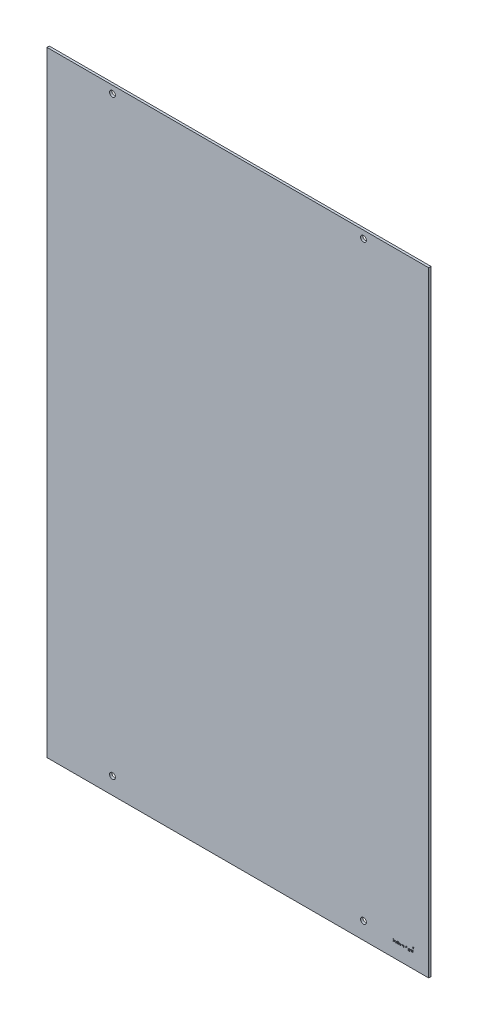
SolidWorks part; units mm, degrees
material "Acrylic (Medium-high impact)"
ref_plane "Front Plane" through (0, 0, 0) normal (0, 0, 1) x (1, 0, 0)
ref_plane "Top Plane" through (0, 0, 0) normal (0, 1, 0) x (1, 0, 0)
ref_plane "Right Plane" through (0, 0, 0) normal (1, 0, 0) x (0, 0, -1)
sketch "Sketch1" plane through (0, 0, 0) normal (0, 0, 1) x (1, 0, 0)
  line L0 (-251.3838, 405.0538) -> (-251.3838, 408.1272) construction
  line L1 (251.3838, -405.0538) -> (-251.3838, -405.0538)
  line L2 (251.3838, -405.0538) -> (251.3838, 405.0538)
  line L3 (251.3838, 405.0538) -> (-251.3838, 405.0538)
  line L4 (-251.3838, -405.0538) -> (-251.3838, 405.0538)
  line L5 (251.3838, -405.0538) -> (-251.3838, 405.0538) construction
  line L6 (251.3838, 405.0538) -> (-251.3838, -405.0538) construction
  point P0 (0, 0)
  dimension "D1" = 502.7676
  dimension "D2" = 3.0734
  dimension "D3" = 813.181
extrude "Boss-Extrude1" add sketch "Sketch1" along normal blind 3.0734
sketch "Sketch2" plane through (0, 0, 0) normal (0, 0, -1) x (-1, 0, 0)
  line L0 (-165.481, 395.1478) -> (165.1254, 395.1478) construction
  line L1 (165.1254, 395.1478) -> (165.1254, -382.8288) construction
  line L2 (165.1254, -382.8288) -> (-165.481, -382.8288) construction
  line L3 (-165.481, -382.8288) -> (-165.481, 395.1478) construction
  line L4 (-251.3838, -405.0538) -> (-251.3838, 405.0538) construction
  line L5 (-251.3838, 405.0538) -> (251.3838, 405.0538) construction
  line L6 (251.3838, -405.0538) -> (-251.3838, -405.0538) construction
  circle A0 centre (-165.481, 395.1478) radius 3.81
  circle A1 centre (165.1254, 395.1478) radius 3.81
  circle A2 centre (165.1254, -382.8288) radius 3.81
  circle A3 centre (-165.481, -382.8288) radius 3.81
  dimension "D1" = 7.62
  dimension "D2" = 85.9028
  dimension "D3" = 9.906
  dimension "D4" = 330.6064
  dimension "D5" = 22.225
extrude "Cut-Extrude1" cut sketch "Sketch2" against normal through all
sketch "Sketch3" plane through (0, 0, 3.0734) normal (0, 0, 1) x (1, 0, 0)
  line L0 (231.0638, -346.5398) -> (231.0638, -405.0538) construction
  line L1 (-251.3838, -405.0538) -> (251.3838, -405.0538) construction
  line L2 (251.3838, -405.0538) -> (251.3838, 405.0538) construction
  line L3 (165.481, -386.6388) -> (231.0638, -386.6388) construction
  line L4 (231.0638, -379.5645) -> (230.0478, -380.8345)
  line L5 (230.0478, -380.8345) -> (230.5558, -380.8345)
  line L6 (230.5558, -380.8345) -> (230.5558, -382.1045)
  line L7 (230.5558, -382.1045) -> (231.5718, -382.1045)
  line L8 (231.5718, -380.8345) -> (231.5718, -382.1045)
  line L9 (232.0798, -380.8345) -> (231.5718, -380.8345)
  line L10 (231.0638, -379.5645) -> (232.0798, -380.8345)
  line L11 (231.0638, -383.3745) -> (226.8098, -383.3745) construction
  circle A1 centre (165.481, -382.8288) radius 3.81 construction
  text T0 "Bottom Right"
  point P13 (231.0638, -382.1045)
  point P18 (231.0638, -382.1045)
  dimension "D1" = 20.32
  dimension "D2" = 1.016
  dimension "D3" = 2.032
  dimension "D4" = 1.27
  dimension "D5" = 1.27
  dimension "D6" = 1.27
extrude "Cut-Extrude2" cut sketch "Sketch3" against normal blind 1.27
equation "\"Height\"= 32in"
equation "\"Width\"= 23in"
equation "\"Depth\"= 20in"
equation "\"Plexi\"= .121in"
equation "\"EBWidth\" = 9in"
equation "\"MagnetThickness\"= 0.125in"
equation "\"MagnetDiameter\"= 12mm"
equation "\"DoorPlexi\" = \"Plexi\""
equation "\"BasePlateThickness\" = 0.5in"
equation "\"BasePlateWidth\" = \"Width\"+\"EBWidth\"-2*\"Plexi\""
equation "\"BasePlateDepth\" = \"TopBarDepth\"+2*\"CornerCube\""
equation "\"Boxsize\" = .75in"
equation "\"BoxsizeHalf\" = \"Boxsize\"/2"
equation "\"Boxinner\" = .625in"
equation "\"CornerCube\" = 0.75in"
equation "\"FingerLength\" = 1.125in"
equation "\"FingerWidth\" = .625in"
equation "\"Cutwidth\"= .016in"
equation "\"Earsize\"= 1in + \"Cutwidth\" /2"
equation "\"Slotsize\" = 1in - \"CutWidth\" / 2"
equation "\"InnerWidth\" = \"Width\" - 2* \"Plexi\""
equation "\"InnerHeight\" = \"Height\" -2 * \"Plexi\""
equation "\"InnerDepth\" = \"Depth\" - 2*\"Plexi\""
equation "\"FrontDoorGap\" = .1in"
equation "\"TopDepth\" = \"Depth\"-\"DoorPlexi\"-\"FrontDoorGap\""
equation "\"TopBarDepth\" = \"Depth\"-\"DoorPlexi\"-\"Plexi\"-2*\"MagnetThickness\"-2*\"CornerCube\""
equation "\"RearNumHoles\" = 4"
equation "\"RearHolesBorder\" = 2.25"
equation "\"RearHoleSpacing\" = (\"Width\" - 2*\"RearHolesBorder\") / (\"RearNumHoles\"-1)"
equation "\"RearBarLength\" = (\"InnerWidth\"-2*\"CornerCube\")"
equation "\"RearTopNumHoles\" = 4"
equation "\"RearTopHolesBorder\" = 3.1"
equation "\"RearTopHolesSpacing\" = (\"Width\" - 2*\"RearTopHolesBorder\") / (\"RearTopNumHoles\"-1)"
equation "\"SideTopNumHoles\" = 4"
equation "\"SideTopHoleOffset\"=\"CornerCube\"+\"FingerLength\"+\"Plexi\"+.5"
equation "\"SideTopHoleSpacing\" = (\"TopBarDepth\"-2*\"SideTopHoleOffset\") / (\"SideTopNumHoles\"-1)"
equation "\"SideHorizNumHoles\" = 4"
equation "\"SideHorizHoleBorder\" = 1.50"
equation "\"SideHorizHoleSpacing\" = (\"TopBarDepth\"-2*\"SideHorizHoleBorder\") / (\"SideHorizNumHoles\"-1)"
equation "\"SideVertBarLength\"=\"Height\"-\"BasePlateThickness\"-2*\"CornerCube\"-\"Plexi\""
equation "\"SideVertNumHoles\" = 4"
equation "\"SideVertHolesBorder\" = \"CornerCube\"+\"FingerLength\"+1.50"
equation "\"SideVertHoleSpacing\" = (\"InnerHeight\" - 2*\"SideVertHolesBorder\") / (\"SideVertNumHoles\"-1)"
equation "\"RearSideVertNumHoles\" = 4"
equation "\"RearSideVertHolesBorder\" = 2.4"
equation "\"RearSideVertHoleSpacing\" = (\"InnerHeight\" - 2*\"RearSideVertHolesBorder\") / (\"RearSideVertNumHoles\"-1)"
equation "\"RivetDia\" = .228in"
equation "\"SlotDepth\" = \"Plexi\" + 0.75in + .005in"
equation "\"SideSlotWidth\"   = \"Plexi\"+.005in"
equation "\"SidePanelVertSpacing\" = (\"Height\"-2*(1.75-\"Plexi\")) / 5"
equation "\"BottomPanelSideHoleSpacing\" = (\"InnerDepth\"-2*(1.75-\"Plexi\")) / 4"
equation "\"CoolerDepth\" = 12in"
equation "\"ShelfGap\" = 0.5in"
equation "\"ShelfDepth\" = \"TopBarDepth\"+\"CornerCube\"-\"CoolerDepth\""
equation "\"ShelfBarDepth\"=\"ShelfDepth\"-2*\"CornerCube\""
equation "\"ShelfWidth\" = \"EBWidth\"-\"ShelfGap\""
equation "\"ShelfBarWidth\" = \"EBWidth\"-\"Boxsize\""
equation "\"ShelfBarWidthShort\" = \"ShelfBarWidth\"-\"Boxsize\"-\"ShelfGap\""
equation "\"IntakeWidth\"=4in"
equation "\"IntakeHeight\"=2in"
equation "\"ExhaustWidth\"=4in"
equation "\"ExhaustHeight\"=2in"
equation "\"VentSpacing\"=7in"
equation "\"AngleBracketLength\"=20mm"
equation "\"AngleBracketWidth\"=.5in"
equation "\"AngleBracketThickness\"=.125in"
equation "\"AngleBracketHolePos\"=15mm"
equation "\"AngleBracketHoleDia\"=\"Rivet3_16Dia\""
equation "\"ShelfBarAngleHole\"=\"ShelfGap\"+\"Boxsize\"+\"AngleBracketHolePosShort\""
equation "\"D1@Sketch1\"=\"TopDepth\"+\"RivNutHeight\""
equation "\"D2@Sketch1\"=\"Plexi\""
equation "\"D3@Sketch1\"=\"Height\"+\"RivNutHeight\""
equation "\"D1@Boss-Extrude1\"=\"Plexi\""
equation "\"ComponentMountDia\"=0.1770"
equation "\"ShelfThickness\" = .1250in"
equation "\"Rivet3_16Dia\" = .191in"
equation "\"BinderPostDia\" = .228in"
equation "\"ShelfHeight1\" = 13in"
equation "\"ShelfHeight2\" = 24in"
equation "\"VentVertLocation\"=12.75in"
equation "\"AngleBracketLengthShort\"=.625in"
equation "\"AngleBracketLengthLong\"=1in"
equation "\"AngleBracketHolePosShort\"=.358in"
equation "\"AngleBracketHolePosLong\"=.7in"
equation "\"PSBracketThickness\" = .0641in"
equation "\"EBForwardMountOffset\" = 4.0in"
equation "\"EBForwardMount\" = 2*\"Boxsize\"+\"CoolerDepth\"+\"EBForwardMountOffset\""
equation "\"EBRearwardMountOffset\" = 1.5in"
equation "\"EBRearwardMount\"= \"Boxsize\"+\"EBRearwardMountOffset\""
equation "\"MagSealWidth\" = \"InnerWidth\""
equation "\"MagSealHeight\" = \"Height\"-\"BasePlateThickness\"-\"Plexi\""
equation "\"MagWidth\" = .500in"
equation "\"SiliconeSealOD\" = .3125in"
equation "\"SiliconeSealID\" = .1875in"
equation "\"SiliconeSealWidth\" = \"MagSealWidth\" - 2*\"MagWidth\"-\"SiliconeSealOD\""
equation "\"SiliconeSealHeigth\" = \"MagSealHeight\" - 2*\"MagWidth\"-\"SiliconeSealOD\""
equation "\"HooknLoopThick\" = .085in"
equation "\"HooknLoopWidth\" = 0.75in"
equation "\"HooknLoopHeigth\" = 0.75in"
equation "\"RivNutHeight\" = 0.015in"
equation "\"D2@Sketch2\"=\"Plexi\"+\"RivNutHeight\"+\"CornerCube\"+\"SideTopHoleOffset\""
equation "\"D3@Sketch2\"=\"RivNutHeight\"+\"BoxsizeHalf\""
equation "\"D4@Sketch2\"=\"SideTopHoleSpacing\"*3"
equation "\"D5@Sketch2\"=\"BasePlateThickness\"+\"BoxsizeHalf\""
